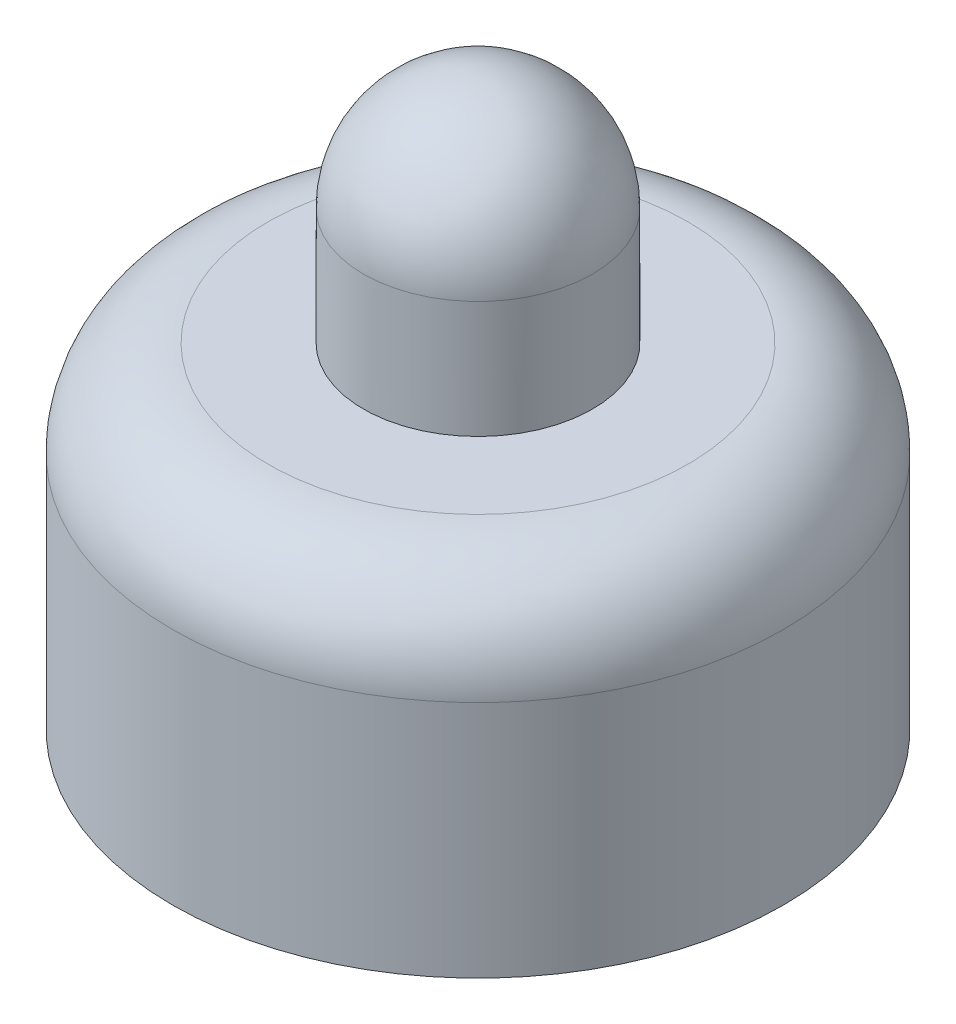
SolidWorks part; units mm, degrees
ref_plane "前视基准面" through (0, 0, 0) normal (0, 0, 1) x (1, 0, 0)
ref_plane "上视基准面" through (0, 0, 0) normal (0, 1, 0) x (1, 0, 0)
ref_plane "右视基准面" through (0, 0, 0) normal (1, 0, 0) x (0, 0, -1)
other "Configuration Table"
sketch "草图1" plane through (0, 0, 0) normal (0, 0, 1) x (1, 0, 0)
  line L0 (0, 0) -> (0, 19.1857)
  line L1 (2.4, 16.7857) -> (2.4, 14.3357)
  line L2 (2.4, 14.3357) -> (6.4, 14.3357)
  line L3 (6.4, 14.3357) -> (6.4, 7.3357)
  line L4 (6.4, 7.3357) -> (0, 7.3357)
  line L5 (0, 0) -> (0, 7.3357)
  arc A0 (2.4, 16.7857) -> (0, 19.1857) centre (0, 16.7857) ccw
  dimension "D1" = 2.4
  dimension "D2" = 2.45
  dimension "D3" = 7
  dimension "D4" = 4
revolve "旋转1" add sketch "草图1" angle 360 about L0
fillet "圆角1" radius 2 1 edges at (0, 14.3357, -6.4)
